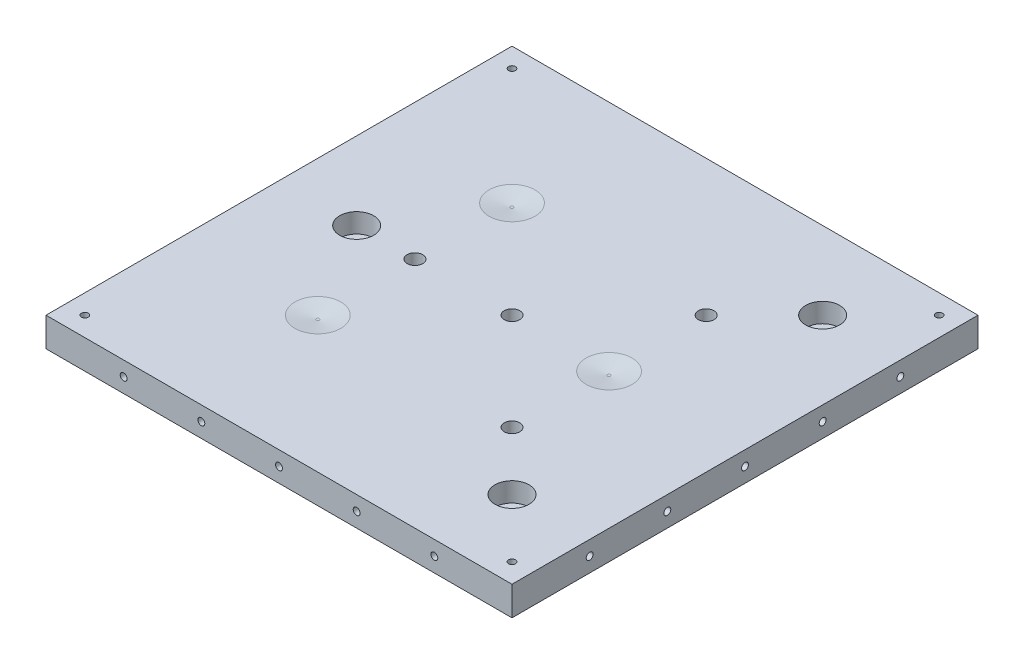
SolidWorks part; units mm, degrees
other "Markup1"
sketch "Sketch11" plane through (-76.2, -0.0001, -76.2) normal (-0.3002, -0.6123, -0.7314) x (0.9434, -0.077, -0.3227)
material "1060 Alloy"
ref_plane "Front Plane" through (0, 0, 0) normal (0, 0, 1) x (1, 0, 0)
ref_plane "Top Plane (Under Plate)" through (0, 0, 0) normal (0, 1, 0) x (1, 0, 0)
ref_plane "Right Plane" through (0, 0, 0) normal (1, 0, 0) x (0, 0, -1)
sketch "Plates_Dims" plane through (0, 0, 0) normal (0, 1, 0) x (1, 0, 0)
  line L1 (-76.2, 76.2) -> (76.2, 76.2)
  line L2 (-76.2, 76.2) -> (-76.2, -76.2)
  line L3 (-76.2, -76.2) -> (76.2, -76.2)
  line L4 (76.2, 76.2) -> (76.2, -76.2)
  line L5 (-76.2, 76.2) -> (76.2, -76.2) construction
  line L6 (-76.2, -76.2) -> (76.2, 76.2) construction
  point P0 (0, 0)
  point P8 (-47.9699, -47.9699)
  dimension "D1" = 152.4
extrude "Plate_Thickness" add sketch "Plates_Dims" along normal blind 9.525
hole_wizard "#4-40 Tapped Hole1" positions "3DSketch1" profile "Sketch2" tap size "#4-40" standard "ANSI Inch" end condition through all
sketch3d "3DSketch1"
  line L2 (-76.2, 9.525, 76.2) -> (76.2, 9.525, 76.2) construction
  line L3 (76.2, 9.525, -76.2) -> (76.2, 9.525, 76.2) construction
  point P0 (69.85, 9.525, 69.85)
  dimension "D1" = 6.35
  dimension "D2" = 6.35
cosmetic thread "Hole Thread1" parameters "D2"=2.8448
sketch "Sketch2" plane through (69.85, 9.525, 69.85) normal (1, 0, 0) x (0, 0, 1)
  line L0 (0, 0) -> (0, 9.525)
  line L1 (0, 9.525) -> (1.1303, 9.525)
  line L2 (1.1303, 9.525) -> (1.1303, 0)
  line L5 (1.1303, 0) -> (0, 0)
  line L11 (0, -6.35) -> (0, 107.95) construction
  dimension "Thru Tap Drill Dia." = 2.2606
  dimension "Thru Tap Drill Depth" = 9.525
pattern_linear "LPattern1" count 2 spacing 139.7 along (0, 0, -1) count 2 spacing 139.7 along (-1, 0, 0) of "#4-40 Tapped Hole1"
cosmetic thread "Hole Thread2" parameters "D2"=2.8448
cosmetic thread "Hole Thread3" parameters "D2"=2.8448
cosmetic thread "Hole Thread4" parameters "D2"=2.8448
hole_wizard "#4-40 Tapped Hole2" [suppressed] positions "3DSketch2" profile "Sketch3" tap size "#4-40" standard "ANSI Inch"
sketch3d "3DSketch2" [suppressed]
  line L2 (76.2, 9.525, -76.2) -> (76.2, 9.525, 76.2) construction
  line L3 (-76.2, 9.525, 76.2) -> (76.2, 9.525, 76.2) construction
  point P0 (63.5, 9.525, 63.5)
  dimension "D1" = 12.7
  dimension "D2" = 12.7
sketch "Sketch3" [suppressed] plane through (63.5, 9.525, 63.5) normal (1, 0, 0) x (0, 0, 1)
  line L0 (0, 0) -> (0, 9.525)
  line L1 (0, 9.525) -> (1.1303, 9.525)
  line L2 (1.1303, 9.525) -> (1.1303, 0)
  line L5 (1.1303, 0) -> (0, 0)
  line L11 (0, -6.35) -> (0, 107.95) construction
  dimension "Thru Tap Drill Dia." = 2.2606
  dimension "Thru Tap Drill Depth" = 9.525
cosmetic thread "Hole Thread5" [suppressed] parameters "D2"=2.8448
pattern_linear "LPattern2" [suppressed] count 6 spacing 25.4 count 6 spacing 25.4
cosmetic thread "Hole Thread6" [suppressed] parameters "D2"=2.8448
cosmetic thread "Hole Thread7" [suppressed] parameters "D2"=2.8448
cosmetic thread "Hole Thread8" [suppressed] parameters "D2"=2.8448
cosmetic thread "Hole Thread9" [suppressed] parameters "D2"=2.8448
cosmetic thread "Hole Thread10" [suppressed] parameters "D2"=2.8448
cosmetic thread "Hole Thread11" [suppressed] parameters "D2"=2.8448
cosmetic thread "Hole Thread12" [suppressed] parameters "D2"=2.8448
cosmetic thread "Hole Thread13" [suppressed] parameters "D2"=2.8448
cosmetic thread "Hole Thread14" [suppressed] parameters "D2"=2.8448
cosmetic thread "Hole Thread15" [suppressed] parameters "D2"=2.8448
cosmetic thread "Hole Thread16" [suppressed] parameters "D2"=2.8448
cosmetic thread "Hole Thread17" [suppressed] parameters "D2"=2.8448
cosmetic thread "Hole Thread18" [suppressed] parameters "D2"=2.8448
cosmetic thread "Hole Thread19" [suppressed] parameters "D2"=2.8448
cosmetic thread "Hole Thread20" [suppressed] parameters "D2"=2.8448
cosmetic thread "Hole Thread21" [suppressed] parameters "D2"=2.8448
cosmetic thread "Hole Thread22" [suppressed] parameters "D2"=2.8448
cosmetic thread "Hole Thread23" [suppressed] parameters "D2"=2.8448
cosmetic thread "Hole Thread24" [suppressed] parameters "D2"=2.8448
cosmetic thread "Hole Thread25" [suppressed] parameters "D2"=2.8448
cosmetic thread "Hole Thread26" [suppressed] parameters "D2"=2.8448
cosmetic thread "Hole Thread27" [suppressed] parameters "D2"=2.8448
cosmetic thread "Hole Thread28" [suppressed] parameters "D2"=2.8448
cosmetic thread "Hole Thread29" [suppressed] parameters "D2"=2.8448
cosmetic thread "Hole Thread30" [suppressed] parameters "D2"=2.8448
cosmetic thread "Hole Thread31" [suppressed] parameters "D2"=2.8448
cosmetic thread "Hole Thread32" [suppressed] parameters "D2"=2.8448
cosmetic thread "Hole Thread33" [suppressed] parameters "D2"=2.8448
cosmetic thread "Hole Thread34" [suppressed] parameters "D2"=2.8448
cosmetic thread "Hole Thread35" [suppressed] parameters "D2"=2.8448
cosmetic thread "Hole Thread36" [suppressed] parameters "D2"=2.8448
cosmetic thread "Hole Thread37" [suppressed] parameters "D2"=2.8448
cosmetic thread "Hole Thread38" [suppressed] parameters "D2"=2.8448
cosmetic thread "Hole Thread39" [suppressed] parameters "D2"=2.8448
cosmetic thread "Hole Thread40" [suppressed] parameters "D2"=2.8448
hole_wizard "#4-40 Tapped Hole3" positions "3DSketch3" profile "Sketch5" tap size "#4-40" standard "ANSI Inch"
sketch3d "3DSketch3"
  line L0 (-76.2, 9.525, 76.2) -> (-76.2, 0, 76.2) construction
  line L1 (-76.2, 0, 76.2) -> (76.2, 0, 76.2) construction
  point P0 (-50.8, 4.7625, 76.2)
  dimension "D2" = 4.7625
  dimension "D1" = 25.4
sketch "Sketch5" plane through (-50.8, 4.7625, 76.2) normal (1, 0, 0) x (0, -1, 0)
  line L0 (0, 0) -> (0, 8.2792)
  line L1 (0, 8.2792) -> (1.1303, 7.6)
  line L2 (1.1303, 7.6) -> (1.1303, 0)
  line L5 (1.1303, 0) -> (0, 0)
  line L10 (0, 8.2792) -> (-1.1303, 7.6) construction
  line L11 (0, -6.35) -> (0, 107.95) construction
  dimension "Tap Drill Dia." = 2.2606
  dimension "Tap Drill Depth" = 7.6
  dimension "Drill Angle" = 118
cosmetic thread "Hole Thread41" parameters "D1"=5.69, "D2"=2.8448
pattern_linear "LPattern3" count 5 spacing 25.4 along (1, 0, 0) of "#4-40 Tapped Hole3"
cosmetic thread "Hole Thread42" parameters "D1"=5.69, "D2"=2.8448
cosmetic thread "Hole Thread43" parameters "D1"=5.69, "D2"=2.8448
cosmetic thread "Hole Thread44" parameters "D1"=5.69, "D2"=2.8448
cosmetic thread "Hole Thread45" parameters "D1"=5.69, "D2"=2.8448
hole_wizard "#4-40 Tapped Hole4" positions "3DSketch4" profile "Sketch6" tap size "#4-40" standard "ANSI Inch"
sketch3d "3DSketch4"
  line L0 (-76.2, 9.525, -76.2) -> (-76.2, 0, -76.2) construction
  line L1 (-76.2, 0, -76.2) -> (-76.2, 0, 76.2) construction
  point P0 (-76.2, 4.7625, -50.8)
  dimension "D2" = 4.7625
  dimension "D1" = 25.4
sketch "Sketch6" plane through (-76.2, 4.7625, -50.8) normal (0, 1, 0) x (0, 0, 1)
  line L0 (0, 0) -> (0, 8.2792)
  line L1 (0, 8.2792) -> (1.1303, 7.6)
  line L2 (1.1303, 7.6) -> (1.1303, 0)
  line L5 (1.1303, 0) -> (0, 0)
  line L10 (0, 8.2792) -> (-1.1303, 7.6) construction
  line L11 (0, -6.35) -> (0, 107.95) construction
  dimension "Tap Drill Dia." = 2.2606
  dimension "Tap Drill Depth" = 7.6
  dimension "Drill Angle" = 118
cosmetic thread "Hole Thread46" parameters "D1"=5.69, "D2"=2.8448
pattern_linear "LPattern4" count 5 spacing 25.4 along (0, 0, 1) of "#4-40 Tapped Hole4"
cosmetic thread "Hole Thread47" parameters "D1"=5.69, "D2"=2.8448
cosmetic thread "Hole Thread48" parameters "D1"=5.69, "D2"=2.8448
cosmetic thread "Hole Thread49" parameters "D1"=5.69, "D2"=2.8448
cosmetic thread "Hole Thread50" parameters "D1"=5.69, "D2"=2.8448
ref_plane "Mid_Plane_X" through (0, 0, 0) normal (-1, 0, 0) x (0, 0, 1)
ref_plane "Mid_Plane_Y" through (0, 0, 0) normal (0, 0, -1) x (-1, 0, 0)
mirror "Mirrior_Y" about plane through (0, 0, 0) normal (0, 0, -1) of "LPattern3", "#4-40 Tapped Hole3"
cosmetic thread "Hole Thread51" parameters "D1"=5.69, "D2"=2.8448
cosmetic thread "Hole Thread52" parameters "D1"=5.69, "D2"=2.8448
cosmetic thread "Hole Thread53" parameters "D1"=5.69, "D2"=2.8448
cosmetic thread "Hole Thread54" parameters "D1"=5.69, "D2"=2.8448
cosmetic thread "Hole Thread55" parameters "D1"=5.69, "D2"=2.8448
mirror "Mirror_X" about plane through (0, 0, 0) normal (-1, 0, 0) of "LPattern4", "#4-40 Tapped Hole4"
cosmetic thread "Hole Thread56" parameters "D1"=5.69, "D2"=2.8448
cosmetic thread "Hole Thread57" parameters "D1"=5.69, "D2"=2.8448
cosmetic thread "Hole Thread58" parameters "D1"=5.69, "D2"=2.8448
cosmetic thread "Hole Thread59" parameters "D1"=5.69, "D2"=2.8448
cosmetic thread "Hole Thread60" parameters "D1"=5.69, "D2"=2.8448
sketch3d "Cone_&_Groove_Plane_Height"
  line L0 (-76.2, 9.525, 76.2) -> (-76.2, 0, 76.2) construction
  line L1 (76.2, 9.525, -76.2) -> (76.2, 0, -76.2) construction
  line L2 (76.2, 9.525, 76.2) -> (76.2, 0, 76.2) construction
  point P0 (-76.2, 6.35, 76.2)
  point P1 (76.2, 6.35, 76.2)
  point P4 (76.2, 6.35, -76.2)
  point P5 (0, 0, 0)
  point P8 (0, 0, 0)
  point P9 (0, 0, 0)
  point P10 (0, 0, 0)
  point P13 (0, 0, 0)
  dimension "D1" = 3.175
ref_plane "Top_Cone_&_Groove_Plane" through (0, 6.35, 0) normal (0, -1, 0) x (-1, 0, 0)
sketch "Top_Cone" plane through (0, 6.35, 0) normal (0, -1, 0) x (-1, 0, 0)
  line L2 (76.2, 76.2) -> (76.2, -76.2) construction
  line L3 (76.2, -76.2) -> (-76.2, -76.2) construction
  circle A0 centre (50.8, -50.8) radius 0.5
  point P2 (49.513, -43.5425)
  dimension "D1" = 25.4
  dimension "D3" = 1
  dimension "D2" = 25.4
sketch "Bottom_Cone" plane through (0, 0, 0) normal (0, 1, 0) x (1, 0, 0)
  line L0 (-76.2, -76.2) -> (76.2, -76.2) construction
  line L1 (-76.2, 76.2) -> (-76.2, -76.2) construction
  circle A0 centre (-50.8, -50.8) radius 8.89
  dimension "D2" = 25.4
  dimension "D1" = 17.78
  dimension "D3" = 25.4
loft "Cone_Cut" cut profiles "Bottom_Cone", "Top_Cone"
sketch "Bottom_Groove" plane through (0, 0, 0) normal (0, 1, 0) x (1, 0, 0)
  line L0 (-76.2, 76.2) -> (-76.2, -76.2) construction
  line L1 (-59.69, 62.7063) -> (-41.91, 62.7062)
  line L2 (-59.69, 62.7063) -> (-59.69, 38.8937)
  line L3 (-59.69, 38.8937) -> (-41.91, 38.8937)
  line L4 (-41.91, 62.7062) -> (-41.91, 38.8937)
  line L5 (-76.2, 76.2) -> (76.2, 76.2) construction
  point P4 (-50.8, 50.8)
  point P5 (0, 0)
  point P6 (-50.8, 62.7062)
  point P7 (-41.91, 50.8)
  point P8 (-42.9237, 42.4048)
  dimension "D3" = 25.4
  dimension "D1" = 17.78
  dimension "D2" = 23.8125
  dimension "D4" = 25.4
sketch "Top_Groove" plane through (0, 6.35, 0) normal (0, -1, 0) x (-1, 0, 0)
  line L0 (76.2, 76.2) -> (-76.2, 76.2) construction
  line L1 (51.3, 62.7062) -> (50.3, 62.7062)
  line L2 (51.3, 62.7062) -> (51.3, 38.8937)
  line L3 (51.3, 38.8937) -> (50.3, 38.8937)
  line L4 (50.3, 62.7062) -> (50.3, 38.8937)
  line L5 (51.3, 62.7062) -> (50.3, 38.8937) construction
  line L6 (51.3, 38.8937) -> (50.3, 62.7062) construction
  line L8 (76.2, 76.2) -> (76.2, -76.2) construction
  point P0 (50.8, 50.8)
  dimension "D1" = 25.4
  dimension "D2" = 25.4
  dimension "D3" = 23.8125
  dimension "D4" = 1
loft "Groove_Cut" cut profiles "Bottom_Groove", "Top_Groove"
sketch "Flat_Dims" plane through (0, 0, 0) normal (0, 1, 0) x (1, 0, 0)
  line L0 (76.2, 76.2) -> (76.2, -76.2) construction
  line L1 (41.275, 9.525) -> (60.325, 9.525)
  line L2 (41.275, 9.525) -> (41.275, -9.525)
  line L3 (41.275, -9.525) -> (60.325, -9.525)
  line L4 (60.325, 9.525) -> (60.325, -9.525)
  line L5 (41.275, 9.525) -> (60.325, -9.525) construction
  line L6 (41.275, -9.525) -> (60.325, 9.525) construction
  line L10 (-76.2, 76.2) -> (76.2, 76.2) construction
  point P0 (50.8, 0)
  point P5 (0, 0)
  point P8 (0, 0)
  point P14 (0, 0)
  dimension "D1" = 25.4
  dimension "D2" = 19.05
  dimension "D3" = 76.2
extrude "Flat_Cut_Length" cut sketch "Flat_Dims" along normal blind 4.7112
hole_wizard "1/4-20 Tapped Hole2" positions "3DSketch12" profile "Sketch16" tap size "1/4-20" standard "ANSI Inch" end condition through all
sketch3d "3DSketch12"
  line L0 (-76.2, 9.525, -76.2) -> (-76.2, 9.525, 76.2) construction
  line L1 (76.2, 9.525, -76.2) -> (76.2, 9.525, 76.2) construction
  line L2 (-76.2, 9.525, 76.2) -> (76.2, 9.525, 76.2) construction
  line L3 (-76.2, 9.525, -76.2) -> (76.2, 9.525, -76.2) construction
  point P0 (-31.75, 9.525, 0)
  point P2 (0, 9.525, 0)
  point P4 (31.75, 9.525, 31.75)
  point P6 (31.75, 9.525, -31.75)
  point P9 (0, 0, 0)
  point P13 (0, 0, 0)
  dimension "D5" = 44.45
  dimension "D1" = 44.45
  dimension "D2" = 44.45
  dimension "D3" = 44.45
  dimension "D4" = 44.45
sketch "Sketch16" plane through (-31.75, 9.525, 0) normal (1, 0, 0) x (0, 0, 1)
  line L0 (0, 0) -> (0, 9.5251)
  line L1 (0, 9.5251) -> (2.5527, 9.5251)
  line L2 (2.5527, 9.5251) -> (2.5527, 0)
  line L5 (2.5527, 0) -> (0, 0)
  line L11 (0, -6.35) -> (0, 107.95) construction
  dimension "Thru Tap Drill Dia." = 5.1054
  dimension "Thru Tap Drill Depth" = 9.5251
cosmetic thread "Hole Thread64" parameters "D2"=6.35
cosmetic thread "Hole Thread65" parameters "D2"=6.35
cosmetic thread "Hole Thread66" parameters "D2"=6.35
cosmetic thread "Hole Thread67" parameters "D2"=6.35
hole_wizard "CBORE for 1/4 Socket Head Cap Screw1" positions "3DSketch9" profile "Sketch15" counterbore size "1/4" standard "ANSI Inch" end condition through all
sketch3d "3DSketch9"
  line L0 (-76.2, 9.525, -76.2) -> (-76.2, 9.525, 76.2) construction
  line L1 (-76.2, 9.525, 76.2) -> (76.2, 9.525, 76.2) construction
  line L2 (76.2, 9.525, -76.2) -> (76.2, 9.525, 76.2) construction
  line L3 (-76.2, 9.525, -76.2) -> (76.2, 9.525, -76.2) construction
  point P0 (-50.8, 9.525, 0)
  point P2 (50.8, 9.525, 50.8)
  point P4 (50.8, 9.525, -50.8)
  point P7 (0, 0, 0)
  point P8 (0, 0, 0)
  point P9 (0, 0, 0)
  dimension "D1" = 25.4
  dimension "D2" = 25.4
  dimension "D3" = 25.4
  dimension "D4" = 25.4
  dimension "D5" = 25.4
sketch "Sketch15" plane through (-50.8, 9.525, 0) normal (1, 0, 0) x (0, 0, 1)
  line L0 (0, 0) -> (0, 9.5251)
  line L1 (0, 9.5251) -> (3.3782, 9.5251)
  line L3 (3.3782, 9.5251) -> (3.3782, 6.35)
  line L4 (3.3782, 6.35) -> (5.5562, 6.35)
  line L5 (5.5562, 6.35) -> (5.5562, 0)
  line L7 (5.5562, 0) -> (0, 0)
  line L11 (0, -6.35) -> (0, 107.95) construction
  dimension "Thru Hole Dia." = 6.7564
  dimension "Thru Hole Depth" = 9.5251
  dimension "C'Bore Dia." = 11.1125
  dimension "C'Bore Depth" = 6.35
ref_plane "Top_Plate_Plane" through (0, 9.525, 0) normal (0, 1, 0) x (1, 0, 0)
sketch3d "Rest_Bottom_Plane_Height"
  line L0 (-76.2, 9.525, -76.2) -> (-76.2, 0, -76.2) construction
  line L1 (-76.2, 9.525, 76.2) -> (-76.2, 0, 76.2) construction
  line L2 (76.2, 9.525, 76.2) -> (76.2, 0, 76.2) construction
  point P0 (-76.2, 8.35, -76.2)
  point P1 (-76.2, 8.35, 76.2)
  point P4 (76.2, 8.35, 76.2)
  point P7 (0, 0, 0)
  point P10 (0, 0, 0)
  point P11 (0, 0, 0)
  point P12 (0, 0, 0)
  point P13 (0, 0, 0)
  dimension "D1" = 2
ref_plane "Rest_Bottom_Plane" through (0, 8.35, 0) normal (0, -1, 0) x (-1, 0, 0)
sketch "Rest_Top_Circle_X" plane through (0, 9.525, 0) normal (0, 1, 0) x (1, 0, 0)
  line L0 (-76.2, 76.2) -> (76.2, 76.2) construction
  line L3 (76.2, 76.2) -> (76.2, -76.2) construction
  circle A2 centre (31.75, 0) radius 7.5
  point P14 (0, 0)
  dimension "D1" = 15
  dimension "D5" = 44.45
  dimension "D6" = 76.2
sketch "Rest_Bottom_Circle_X" plane through (0, 8.35, 0) normal (0, -1, 0) x (-1, 0, 0)
  circle A0 centre (-31.75, 0) radius 0.5
  point P9 (0, 0)
  point P11 (0, 0)
  point P12 (0, 0)
  point P13 (0, 0)
  dimension "D1" = 1
loft "Cut-Loft8" cut profiles "Rest_Top_Circle_X", "Rest_Bottom_Circle_X"
sketch "Rest_Bottom_Circle_X-Z+" plane through (0, 8.35, 0) normal (0, -1, 0) x (-1, 0, 0)
  line L0 (76.2, -76.2) -> (-76.2, -76.2) construction
  line L1 (76.2, 76.2) -> (76.2, -76.2) construction
  circle A0 centre (31.75, -31.75) radius 0.5
  dimension "D3" = 1
  dimension "D1" = 44.45
  dimension "D2" = 44.45
sketch "Rest_Top_Circle_X-Z+" plane through (0, 9.525, 0) normal (0, 1, 0) x (1, 0, 0)
  line L0 (-76.2, -76.2) -> (76.2, -76.2) construction
  line L1 (-76.2, 76.2) -> (-76.2, -76.2) construction
  circle A0 centre (-31.75, -31.75) radius 7.5
  dimension "D1" = 44.45
  dimension "D2" = 44.45
  dimension "D3" = 15
sketch "Rest_Bottom_Circle_X-Z-" plane through (0, 8.35, 0) normal (0, -1, 0) x (-1, 0, 0)
  line L0 (76.2, 76.2) -> (-76.2, 76.2) construction
  line L1 (76.2, 76.2) -> (76.2, -76.2) construction
  circle A0 centre (31.75, 31.75) radius 0.5
  dimension "D3" = 1
  dimension "D1" = 44.45
  dimension "D2" = 44.45
sketch "Rest_Top_Circle_X-Z-" plane through (0, 9.525, 0) normal (0, 1, 0) x (1, 0, 0)
  line L0 (-76.2, 76.2) -> (76.2, 76.2) construction
  line L1 (-76.2, 76.2) -> (-76.2, -76.2) construction
  circle A0 centre (-31.75, 31.75) radius 7.5
  dimension "D1" = 44.45
  dimension "D2" = 44.45
  dimension "D3" = 15
loft "Cut-Loft9" cut profiles "Rest_Bottom_Circle_X-Z+", "Rest_Top_Circle_X-Z+"
loft "Cut-Loft10" cut profiles "Rest_Bottom_Circle_X-Z-", "Rest_Top_Circle_X-Z-"
equation "\"var_depth\"=9.525"
equation "\"D1@Plate_Thickness\" = \"var_depth\""
equation "\"D2@3DSketch3\"=\"var_depth\"/2"
equation "\"D2@3DSketch4\"=\"var_depth\"/2"
equation "\"Bottom_Cone_Dia\" = 17.78"
equation "\"Top_Cone_Dia\" = 1"
equation "\"D3@Top_Cone\" = \"Top_Cone_Dia\""
equation "\"D1@Bottom_Cone\" = \"Bottom_Cone_Dia\""
equation "\"Cone_Distance\"=25.4"
equation "\"D2@Bottom_Cone\" = \"Cone_Distance\""
equation "\"D3@Bottom_Cone\" = \"Cone_Distance\""
equation "\"D1@Top_Cone\" = \"Cone_Distance\""
equation "\"D2@Top_Cone\" = \"Cone_Distance\""
equation "\"Ball_Dia\"= 15.875"
equation "\"D2@Bottom_Groove\" = \"Ball_Dia\" * 1.5"
equation "\"Groove_Distance\"=25.4"
equation "\"D3@Bottom_Groove\" = \"Groove_Distance\""
equation "\"D4@Bottom_Groove\" = \"Groove_Distance\""
equation "\"D1@Top_Groove\" = \"Groove_Distance\""
equation "\"D2@Top_Groove\" = \"Groove_Distance\""
equation "\"D3@Top_Groove\" = \"Ball_Dia\" * 1.5"
equation "\"Flat_Distance\"=25.4"
equation "\"D1@Flat_Dims\" = \"Flat_Distance\""
equation "\"D2@Flat_Dims\"=\"Ball_Dia\" * 1.2"
equation "\"D1@Flat_Cut_Length\" =  ( 1 / 8 )  * 25.4 - 0.004442"
equation "\"Nylon_Distance\"=25.4"
equation "\"D1@3DSketch9\"=\"Nylon_Distance\""
equation "\"D2@3DSketch9\"=\"Nylon_Distance\""
equation "\"D3@3DSketch9\"=\"Nylon_Distance\""
equation "\"D4@3DSketch9\"=\"Nylon_Distance\""
equation "\"D5@3DSketch9\"=\"Nylon_Distance\""
equation "\"Plate_Dim\"=152.4"
equation "\"D1@Plates_Dims\"=\"Plate_Dim\""
equation "\"D3@Flat_Dims\"=\"Plate_Dim\"/2"
equation "\"Sphere_Resting_Loc\" = 44.45"
equation "\"D5@Rest_Top_Circle_X\" = \"Sphere_Resting_Loc\""
equation "\"D6@Rest_Top_Circle_X\" = \"Plate_Dim\" / 2"
equation "\"Thickness_between_Cone_Planes\"=2"
equation "\"D1@Rest_Bottom_Plane_Height\" = \"Thickness_between_Cone_Planes\""
equation "\"Top_Rest_Dia\"=15"
equation "\"D1@Rest_Top_Circle_X\" = \"Top_Rest_Dia\""
equation "\"Bottom_Rest_Dia\"=1"
equation "\"D1@Rest_Bottom_Circle_X\" = \"Bottom_Rest_Dia\""
equation "\"D1@Rest_Bottom_Circle_X-Z+\" = \"Sphere_Resting_Loc\""
equation "\"D2@Rest_Bottom_Circle_X-Z+\" = \"Sphere_Resting_Loc\""
equation "\"D3@Rest_Bottom_Circle_X-Z+\" = \"Bottom_Rest_Dia\""
equation "\"D1@Rest_Top_Circle_X-Z+\" = \"Sphere_Resting_Loc\""
equation "\"D2@Rest_Top_Circle_X-Z+\" = \"Sphere_Resting_Loc\""
equation "\"D1@Rest_Bottom_Circle_X-Z-\" = \"Sphere_Resting_Loc\""
equation "\"D1@Rest_Top_Circle_X-Z-\" = \"Sphere_Resting_Loc\""
equation "\"D2@Rest_Top_Circle_X-Z-\" = \"Sphere_Resting_Loc\""
equation "\"D3@Rest_Top_Circle_X-Z-\" = \"Top_Rest_Dia\""
equation "\"Nylon_Thread_Loc\"= 30.75 + 13.7'13.7 is distance between 4K & 40K plate edges in Assembly"
equation "\"D1@3DSketch12\"=\"Nylon_Thread_Loc\""
equation "\"D2@3DSketch12\"=\"Nylon_Thread_Loc\""
equation "\"D3@3DSketch12\"=\"Nylon_Thread_Loc\""
equation "\"D4@3DSketch12\"=\"Nylon_Thread_Loc\""
equation "\"D5@3DSketch12\"=\"Nylon_Thread_Loc\""
